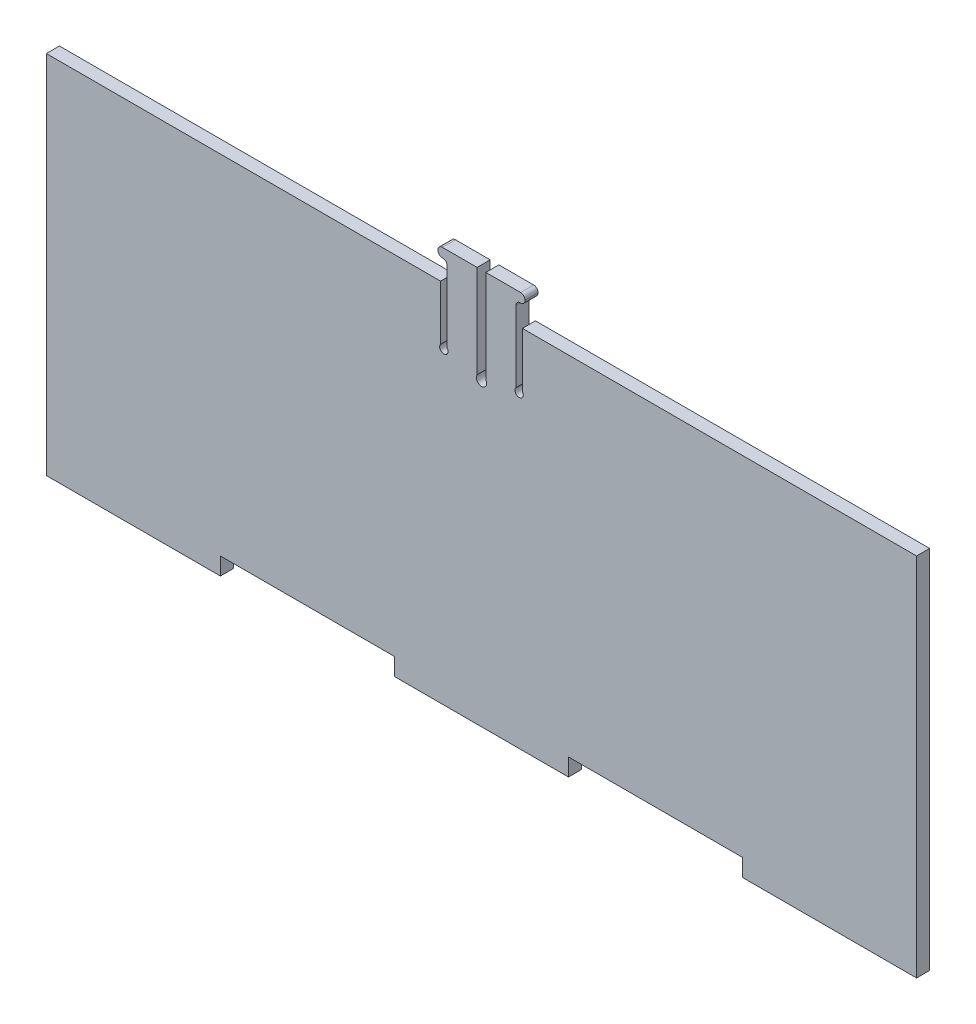
SolidWorks part; units mm, degrees
ref_plane "Front Plane" through (0, 0, 0) normal (0, 0, 1) x (1, 0, 0)
ref_plane "Top Plane" through (0, 0, 0) normal (0, 1, 0) x (1, 0, 0)
ref_plane "Right Plane" through (0, 0, 0) normal (1, 0, 0) x (0, 0, -1)
sketch "Sketch1" plane through (0, 0, 0) normal (0, 0, 1) x (1, 0, 0)
  line L0 (-20, -42) -> (-20, -38)
  line L1 (100, -42) -> (60, -42)
  line L2 (100, -42) -> (100, 42)
  line L3 (100, 42) -> (9.4, 42)
  line L4 (-100, -42) -> (-100, 42)
  line L5 (100, -42) -> (-100, 42) construction
  line L6 (100, 42) -> (-100, -42) construction
  line L7 (-100, -42) -> (-60, -42)
  line L8 (-100, -42) -> (-100, -38)
  line L10 (-60, -42) -> (-60, -38)
  line L11 (20, -42) -> (20, -38)
  line L12 (60, -42) -> (60, -38)
  line L13 (100, -42) -> (100, -38)
  line L14 (-60, -38) -> (-20, -38)
  line L15 (-60, -42) -> (-100, -42)
  line L16 (20, -38) -> (60, -38)
  line L17 (20, -42) -> (-20, -42)
  line L18 (0, 0) -> (0, 53.8785)
  line L19 (-9.4, 42) -> (-100, 42)
  line L20 (1, 27.5834) -> (1, 48.9393)
  line L21 (1, 48.9393) -> (9, 48.9393)
  line L22 (10, 47.9393) -> (10, 47.8393)
  line L23 (9, 46.8393) -> (8.9, 46.8393)
  line L24 (7.9, 45.8393) -> (7.9, 29.438)
  line L25 (-9.4, 29.438) -> (-9.4, 42)
  line L26 (9.4, 29.438) -> (9.4, 42)
  line L29 (-7.9, 45.8393) -> (-7.9, 29.438)
  line L30 (-9, 46.8393) -> (-8.9, 46.8393)
  line L31 (-10, 47.9393) -> (-10, 47.8393)
  line L32 (-1, 48.9393) -> (-9, 48.9393)
  line L33 (-1, 27.5834) -> (-1, 48.9393)
  arc A0 (10, 47.8393) -> (9, 46.8393) centre (9, 47.8393) cw
  arc A1 (9, 48.9393) -> (10, 47.9393) centre (9, 47.9393) cw
  arc A2 (8.9, 46.8393) -> (7.9, 45.8393) centre (8.9, 45.8393) ccw
  arc A3 (-1, 27.5834) -> (1, 27.5834) centre (0, 26.9393) ccw
  arc A4 (7.9, 29.438) -> (9.4, 29.438) centre (8.65, 28.8393) ccw
  arc A5 (-7.9, 29.438) -> (-9.4, 29.438) centre (-8.65, 28.8393) cw
  arc A6 (-8.9, 46.8393) -> (-7.9, 45.8393) centre (-8.9, 45.8393) cw
  arc A7 (-9, 48.9393) -> (-10, 47.9393) centre (-9, 47.9393) ccw
  arc A8 (-10, 47.8393) -> (-9, 46.8393) centre (-9, 47.8393) ccw
  point P0 (0, 0)
  point P28 (10, 46.8393)
  point P31 (10, 48.9393)
  point P34 (7.9, 46.8393)
  point P58 (-7.9, 46.8393)
  point P59 (-10, 48.9393)
  point P60 (-10, 46.8393)
  dimension "D12" = 1
  dimension "D13" = 1
  dimension "D1" = 200
  dimension "D2" = 84
  dimension "D3" = 40
  dimension "D4" = 4
  dimension "D8" = 9
  dimension "D9" = 2.1
  dimension "D10" = 2.1
  dimension "D5" = 5
extrude "Boss-Extrude1" add sketch "Sketch1" along normal blind 3 contours L17 L11 L16 L12 L1 L2 L3 L4 L7 L10 L14 L0
